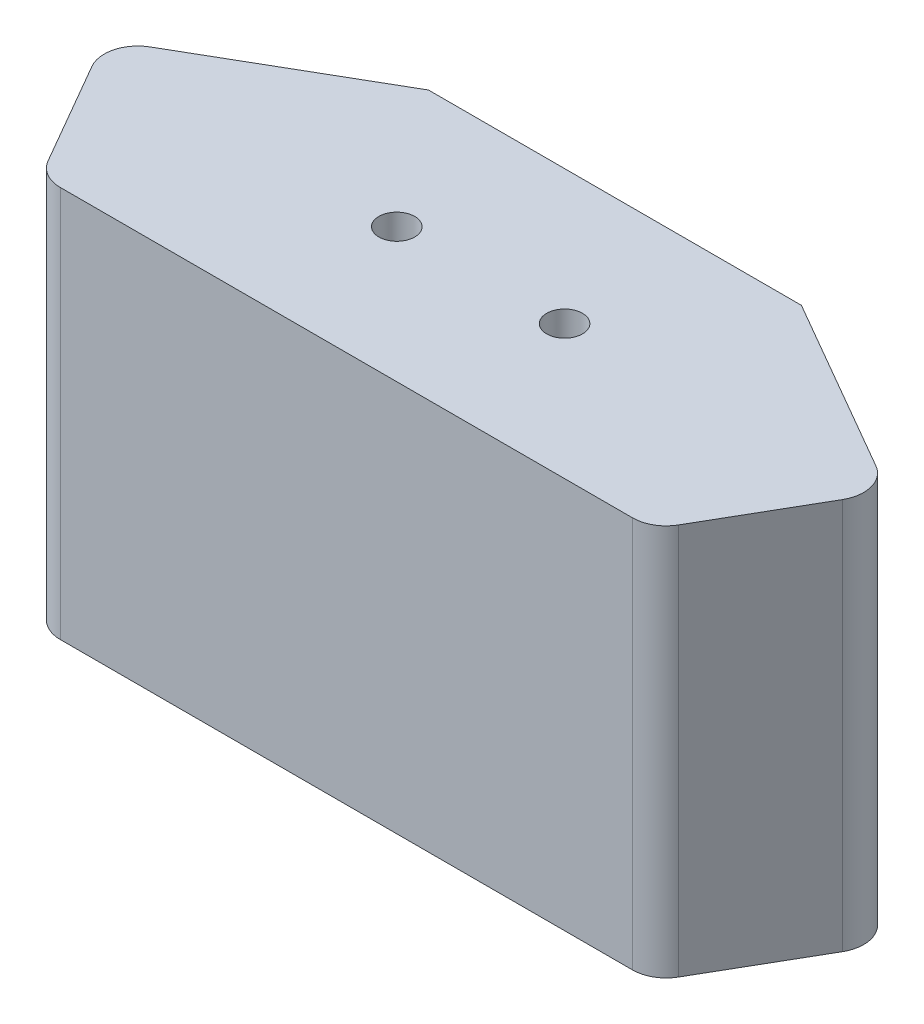
SolidWorks part; units mm, degrees
ref_plane "前基準面" through (0, 0, 0) normal (0, 0, 1) x (1, 0, 0)
ref_plane "上基準面" through (0, 0, 0) normal (0, 1, 0) x (1, 0, 0)
ref_plane "右基準面" through (0, 0, 0) normal (1, 0, 0) x (0, 0, -1)
ref_plane "平面1" through (0, 35, 0) normal (0, 1, 0) x (1, 0, 0)
sketch "草圖1" plane through (0, 35, 0) normal (0, 1, 0) x (1, 0, 0)
  line L0 (8.3333, 20) -> (-7.4429, 10.8916)
  line L1 (-8.541, 6.7935) -> (-3.1754, -2.5)
  line L2 (-0.5774, -4) -> (50.5774, -4)
  line L3 (53.1754, -2.5) -> (58.541, 6.7935)
  line L4 (57.4429, 10.8916) -> (41.6667, 20)
  line L5 (41.6667, 20) -> (8.3333, 20)
  arc A0 (-7.4429, 10.8916) -> (-8.541, 6.7935) centre (-5.9429, 8.2935) ccw
  arc A1 (-3.1754, -2.5) -> (-0.5774, -4) centre (-0.5774, -1) ccw
  arc A2 (50.5774, -4) -> (53.1754, -2.5) centre (50.5774, -1) ccw
  arc A3 (58.541, 6.7935) -> (57.4429, 10.8916) centre (55.9429, 8.2935) ccw
extrude "填料-伸長1" add sketch "草圖1" against normal blind 35
hole_wizard "M3 平頭機械螺釘的錐孔1" positions "草圖3" profile "草圖2" countersink size "M3" standard "Ansi Metric"
sketch "草圖3" plane through (0, 0, 0) normal (0, -1, 0) x (-1, 0, 0)
  point P0 (-17.5, 8)
  point P1 (-32.5, 8)
sketch "草圖2" plane through (17.5, 0, -8) normal (1, 0, 0) x (0, 0, -1)
  line L0 (0, 0) -> (0, 35)
  line L1 (0, 35) -> (1.6, 35)
  line L2 (1.6, 35) -> (1.6, 28.7)
  line L3 (1.6, 28.7) -> (3.3, 27)
  line L4 (3.3, 27) -> (3.3, 0)
  line L6 (3.3, 0) -> (0, 0)
  line L7 (-1.6, 28.7) -> (-3.3, 27) construction
  line L11 (0, -6.35) -> (0, 107.95) construction
  dimension "砮 ふ 畖" = 3.2
  dimension "砮 ふ瞏 " = 35
  dimension "繞ふ 畖" = 6.6
  dimension "繞ふà " = 90
  dimension "繷狠緇回" = 27
